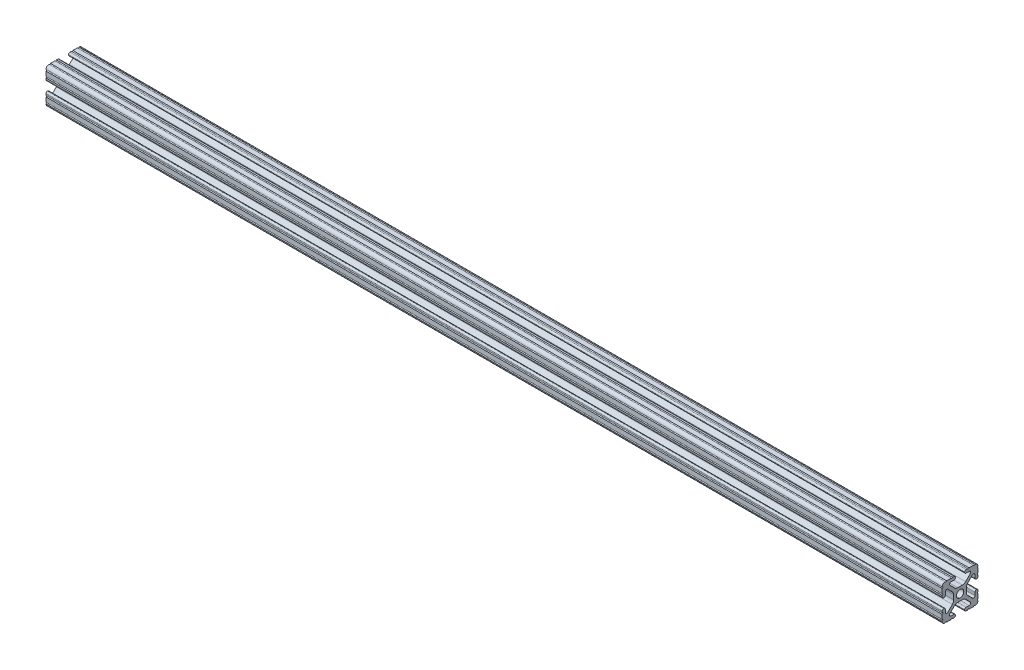
SolidWorks part; units mm, degrees
material "6061-T6 (SS)"
ref_plane "Front Plane" through (0, 0, 0) normal (0, 0, 1) x (1, 0, 0)
ref_plane "Top Plane" through (0, 0, 0) normal (0, 1, 0) x (1, 0, 0)
ref_plane "Right Plane" through (0, 0, 0) normal (1, 0, 0) x (0, 0, -1)
sketch "Sketch1" plane through (0, 0, 0) normal (1, 0, 0) x (0, 0, -1)
  line L0 (6.3331, -12.7) -> (9.5504, -12.7)
  line L1 (12.7, -9.5504) -> (12.7, -6.3331)
  line L2 (12.7, -5.3171) -> (12.7, -4.2875)
  line L3 (11.651, -3.2385) -> (11.5392, -3.2385)
  line L4 (10.4902, -4.2875) -> (10.4902, -6.4021)
  line L5 (8.7371, -7.1294) -> (5.441, -3.8408)
  line L6 (4.5085, -1.5932) -> (4.5085, 1.5932)
  line L7 (5.441, 3.8408) -> (8.7371, 7.1294)
  line L8 (10.4902, 6.4021) -> (10.4902, 4.2875)
  line L9 (11.5392, 3.2385) -> (11.651, 3.2385)
  line L10 (12.7, 4.2875) -> (12.7, 5.3171)
  line L11 (12.7, 6.3331) -> (12.7, 9.5504)
  line L12 (9.5504, 12.7) -> (6.3331, 12.7)
  line L13 (5.3171, 12.7) -> (4.2875, 12.7)
  line L14 (3.2385, 11.651) -> (3.2385, 11.5392)
  line L15 (4.2875, 10.4902) -> (6.4768, 10.4902)
  line L16 (7.207, 8.7244) -> (3.8983, 5.4232)
  line L17 (1.6558, 4.4958) -> (-1.6558, 4.4958)
  line L18 (-3.8983, 5.4232) -> (-7.207, 8.7244)
  line L19 (-6.4768, 10.4902) -> (-4.2875, 10.4902)
  line L20 (-3.2385, 11.5392) -> (-3.2385, 11.651)
  line L21 (-4.2875, 12.7) -> (-5.3171, 12.7)
  line L22 (-6.3331, 12.7) -> (-9.5504, 12.7)
  line L23 (-12.7, 9.5504) -> (-12.7, 6.3331)
  line L24 (-12.7, 5.3171) -> (-12.7, 4.2875)
  line L25 (-11.651, 3.2385) -> (-11.5392, 3.2385)
  line L26 (-10.4902, 4.2875) -> (-10.4902, 6.4021)
  line L27 (-8.7371, 7.1294) -> (-5.441, 3.8408)
  line L28 (-4.5085, 1.5932) -> (-4.5085, -1.5932)
  line L29 (-5.441, -3.8408) -> (-8.7371, -7.1294)
  line L30 (-10.4902, -6.4021) -> (-10.4902, -4.2875)
  line L31 (-11.5392, -3.2385) -> (-11.651, -3.2385)
  line L32 (-12.7, -4.2875) -> (-12.7, -5.3171)
  line L33 (-12.7, -6.3331) -> (-12.7, -9.5504)
  line L34 (-9.5504, -12.7) -> (-6.3331, -12.7)
  line L35 (-5.3171, -12.7) -> (-4.2875, -12.7)
  line L36 (-3.2385, -11.651) -> (-3.2385, -11.5392)
  line L37 (-4.2875, -10.4902) -> (-6.4164, -10.4902)
  line L38 (-7.1797, -8.6452) -> (-3.9523, -5.4237)
  line L39 (-1.7093, -4.4958) -> (1.7093, -4.4958)
  line L40 (3.9523, -5.4237) -> (7.1797, -8.6452)
  line L41 (6.4164, -10.4902) -> (4.2875, -10.4902)
  line L42 (3.2385, -11.5392) -> (3.2385, -11.651)
  line L43 (4.2875, -12.7) -> (5.3171, -12.7)
  circle A0 centre (0, 0) radius 2.6035
  arc A1 (6.3331, -12.7) -> (5.3171, -12.7) centre (5.8251, -12.7) ccw
  arc A2 (10.5664, -12.6998) -> (9.5504, -12.7) centre (10.0584, -12.7) ccw
  arc A3 (10.5664, -12.6998) -> (12.6998, -10.5664) centre (10.5918, -10.5918) ccw
  arc A4 (12.7, -9.5504) -> (12.6998, -10.5664) centre (12.7, -10.0584) ccw
  arc A5 (12.7, -5.3171) -> (12.7, -6.3331) centre (12.7, -5.8251) ccw
  arc A6 (12.7, -4.2875) -> (11.651, -3.2385) centre (11.651, -4.2875) ccw
  arc A7 (11.5392, -3.2385) -> (10.4902, -4.2875) centre (11.5392, -4.2875) ccw
  arc A8 (8.7371, -7.1294) -> (10.4902, -6.4021) centre (9.4628, -6.4021) ccw
  arc A9 (5.441, 3.8408) -> (4.5085, 1.5932) centre (7.6835, 1.5932) ccw
  arc A10 (10.4902, 6.4021) -> (8.7371, 7.1294) centre (9.4628, 6.4021) ccw
  arc A11 (10.4902, 4.2875) -> (11.5392, 3.2385) centre (11.5392, 4.2875) ccw
  arc A12 (11.651, 3.2385) -> (12.7, 4.2875) centre (11.651, 4.2875) ccw
  arc A13 (12.7, 6.3331) -> (12.7, 5.3171) centre (12.7, 5.8251) ccw
  arc A14 (12.6998, 10.5664) -> (12.7, 9.5504) centre (12.7, 10.0584) ccw
  arc A15 (12.6998, 10.5664) -> (10.5664, 12.6998) centre (10.5918, 10.5918) ccw
  arc A16 (9.5504, 12.7) -> (10.5664, 12.6998) centre (10.0584, 12.7) ccw
  arc A17 (5.3171, 12.7) -> (6.3331, 12.7) centre (5.8251, 12.7) ccw
  arc A18 (4.2875, 12.7) -> (3.2385, 11.651) centre (4.2875, 11.651) ccw
  arc A19 (3.2385, 11.5392) -> (4.2875, 10.4902) centre (4.2875, 11.5392) ccw
  arc A20 (7.207, 8.7244) -> (6.4768, 10.4902) centre (6.4768, 9.4563) ccw
  arc A21 (1.6558, 4.4958) -> (3.8983, 5.4232) centre (1.6558, 7.6708) ccw
  arc A22 (-3.8983, 5.4232) -> (-1.6558, 4.4958) centre (-1.6558, 7.6708) ccw
  arc A23 (-6.4768, 10.4902) -> (-7.207, 8.7244) centre (-6.4768, 9.4563) ccw
  arc A24 (-4.2875, 10.4902) -> (-3.2385, 11.5392) centre (-4.2875, 11.5392) ccw
  arc A25 (-3.2385, 11.651) -> (-4.2875, 12.7) centre (-4.2875, 11.651) ccw
  arc A26 (-6.3331, 12.7) -> (-5.3171, 12.7) centre (-5.8251, 12.7) ccw
  arc A27 (-10.5664, 12.6998) -> (-9.5504, 12.7) centre (-10.0584, 12.7) ccw
  arc A28 (-10.5664, 12.6998) -> (-12.6998, 10.5664) centre (-10.5918, 10.5918) ccw
  arc A29 (-12.7, 9.5504) -> (-12.6998, 10.5664) centre (-12.7, 10.0584) ccw
  arc A30 (-12.7, 5.3171) -> (-12.7, 6.3331) centre (-12.7, 5.8251) ccw
  arc A31 (-12.7, 4.2875) -> (-11.651, 3.2385) centre (-11.651, 4.2875) ccw
  arc A32 (-11.5392, 3.2385) -> (-10.4902, 4.2875) centre (-11.5392, 4.2875) ccw
  arc A33 (-8.7371, 7.1294) -> (-10.4902, 6.4021) centre (-9.4628, 6.4021) ccw
  arc A34 (-4.5085, 1.5932) -> (-5.441, 3.8408) centre (-7.6835, 1.5932) ccw
  arc A35 (-5.441, -3.8408) -> (-4.5085, -1.5932) centre (-7.6835, -1.5932) ccw
  arc A36 (-10.4902, -6.4021) -> (-8.7371, -7.1294) centre (-9.4628, -6.4021) ccw
  arc A37 (-10.4902, -4.2875) -> (-11.5392, -3.2385) centre (-11.5392, -4.2875) ccw
  arc A38 (-11.651, -3.2385) -> (-12.7, -4.2875) centre (-11.651, -4.2875) ccw
  arc A39 (-12.7, -6.3331) -> (-12.7, -5.3171) centre (-12.7, -5.8251) ccw
  arc A40 (-12.6998, -10.5664) -> (-12.7, -9.5504) centre (-12.7, -10.0584) ccw
  arc A41 (-12.6998, -10.5664) -> (-10.5664, -12.6998) centre (-10.5918, -10.5918) ccw
  arc A42 (-9.5504, -12.7) -> (-10.5664, -12.6998) centre (-10.0584, -12.7) ccw
  arc A43 (-5.3171, -12.7) -> (-6.3331, -12.7) centre (-5.8251, -12.7) ccw
  arc A44 (-4.2875, -12.7) -> (-3.2385, -11.651) centre (-4.2875, -11.651) ccw
  arc A45 (-3.2385, -11.5392) -> (-4.2875, -10.4902) centre (-4.2875, -11.5392) ccw
  arc A46 (-7.1797, -8.6452) -> (-6.4164, -10.4902) centre (-6.4164, -9.4098) ccw
  arc A47 (-1.7093, -4.4958) -> (-3.9523, -5.4237) centre (-1.7093, -7.6708) ccw
  arc A48 (3.9523, -5.4237) -> (1.7093, -4.4958) centre (1.7093, -7.6708) ccw
  arc A49 (6.4164, -10.4902) -> (7.1797, -8.6452) centre (6.4164, -9.4098) ccw
  arc A50 (4.2875, -10.4902) -> (3.2385, -11.5392) centre (4.2875, -11.5392) ccw
  arc A51 (3.2385, -11.651) -> (4.2875, -12.7) centre (4.2875, -11.651) ccw
  arc A52 (5.441, -3.8408) -> (4.5085, -1.5932) centre (7.6835, -1.5932) cw
  dimension "D1" = 3.175
extrude "Boss-Extrude1" add sketch "Sketch1" along normal mid plane 635
